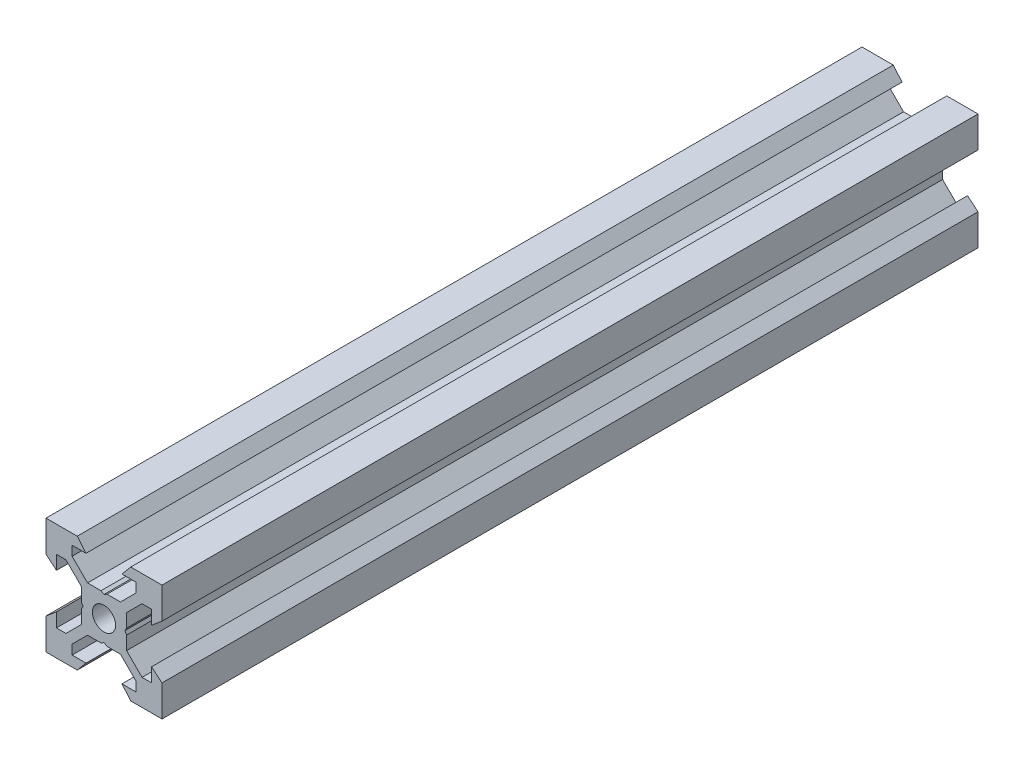
SolidWorks part; units mm, degrees
ref_plane "Front Plane" through (0, 0, 0) normal (0, 0, 1) x (1, 0, 0)
ref_plane "Top Plane" through (0, 0, 0) normal (0, 1, 0) x (1, 0, 0)
ref_plane "Right Plane" through (0, 0, 0) normal (1, 0, 0) x (0, 0, -1)
sketch "Sketch1" plane through (0, 0, 0) normal (0, 0, 1) x (1, 0, 0)
  line L0 (10, 10) -> (4.6104, 10) construction
  line L1 (10, 10) -> (10, 4.6104) construction
  line L2 (10, -10) -> (10, -4.6104) construction
  line L3 (10, -10) -> (4.6104, -10) construction
  line L4 (10, 10) -> (10, 4.6104)
  line L5 (6.5607, 5.5) -> (8.2, 5.5)
  line L6 (5.5, 8.2) -> (5.5, 6.5607)
  line L7 (10, 10) -> (4.6104, 10)
  line L8 (10, 10) -> (10, 4.6104)
  line L9 (6.5607, 5.5) -> (3.9, 2.8393)
  line L10 (5.5, 6.5607) -> (2.8393, 3.9)
  line L11 (10, 4.6104) -> (8.2, 3.1)
  line L12 (4.6104, 10) -> (3.1, 8.2)
  line L13 (8.2, 3.1) -> (8.2, 5.5)
  line L14 (3.1, 8.2) -> (5.5, 8.2)
  line L15 (-6.5607, 5.5) -> (-8.2, 5.5)
  line L16 (6.5607, -5.5) -> (8.2, -5.5)
  line L17 (3.1, -8.2) -> (5.5, -8.2)
  line L18 (8.2, -3.1) -> (8.2, -5.5)
  line L19 (4.6104, -10) -> (3.1, -8.2)
  line L20 (10, -4.6104) -> (8.2, -3.1)
  line L21 (0.5196, -3.9) -> (0, -3.6)
  line L22 (0.5196, 3.9) -> (0, 3.6)
  line L23 (3.6, 0) -> (3.9, -0.5196)
  line L24 (3.9, 0.5196) -> (3.6, 0)
  line L25 (3.9, 0.5196) -> (3.9, 2.8393)
  line L26 (2.8393, 3.9) -> (0.5196, 3.9)
  line L27 (3.9, -2.8393) -> (3.9, -0.5196)
  line L28 (2.8393, -3.9) -> (0.5196, -3.9)
  line L29 (5.5, -6.5607) -> (2.8393, -3.9)
  line L30 (6.5607, -5.5) -> (3.9, -2.8393)
  line L31 (10, -10) -> (10, -4.6104)
  line L32 (10, -10) -> (4.6104, -10)
  line L33 (5.5, -8.2) -> (5.5, -6.5607)
  line L34 (-6.5607, -5.5) -> (-8.2, -5.5)
  line L35 (10, -10) -> (10, -4.6104)
  line L36 (0, 0) -> (0, 8.2) construction
  line L37 (-10, -10) -> (-4.6104, -10) construction
  line L38 (-10, -10) -> (-10, -4.6104) construction
  line L39 (-10, 10) -> (-10, 4.6104) construction
  line L40 (-10, 10) -> (-4.6104, 10) construction
  line L41 (-10, -10) -> (-10, -4.6104)
  line L43 (-5.5, -8.2) -> (-5.5, -6.5607)
  line L44 (-10, -10) -> (-4.6104, -10)
  line L45 (-10, -10) -> (-10, -4.6104)
  line L46 (-6.5607, -5.5) -> (-3.9, -2.8393)
  line L47 (-5.5, -6.5607) -> (-2.8393, -3.9)
  line L48 (-2.8393, -3.9) -> (-0.5196, -3.9)
  line L49 (-3.9, -2.8393) -> (-3.9, -0.5196)
  line L50 (-2.8393, 3.9) -> (-0.5196, 3.9)
  line L51 (-3.9, 0.5196) -> (-3.9, 2.8393)
  line L52 (-3.9, 0.5196) -> (-3.6, 0)
  line L53 (-3.6, 0) -> (-3.9, -0.5196)
  line L54 (-0.5196, 3.9) -> (0, 3.6)
  line L55 (-0.5196, -3.9) -> (0, -3.6)
  line L56 (-10, -4.6104) -> (-8.2, -3.1)
  line L57 (-4.6104, -10) -> (-3.1, -8.2)
  line L58 (-8.2, -3.1) -> (-8.2, -5.5)
  line L59 (-3.1, -8.2) -> (-5.5, -8.2)
  line L60 (-10, -10) -> (10, -10) construction
  line L61 (-10, -10) -> (-10, 10) construction
  line L62 (-3.1, 8.2) -> (-5.5, 8.2)
  line L63 (-8.2, 3.1) -> (-8.2, 5.5)
  line L64 (-4.6104, 10) -> (-3.1, 8.2)
  line L65 (-10, 4.6104) -> (-8.2, 3.1)
  line L66 (-5.5, 6.5607) -> (-2.8393, 3.9)
  line L67 (-6.5607, 5.5) -> (-3.9, 2.8393)
  line L68 (-10, 10) -> (-10, 4.6104)
  line L69 (-10, 10) -> (-4.6104, 10)
  line L70 (-5.5, 8.2) -> (-5.5, 6.5607)
  line L71 (-10, 10) -> (10, 10) construction
  line L72 (-10, 10) -> (-10, 4.6104)
  line L73 (10, -10) -> (10, 10) construction
  line L74 (-10, -10) -> (10, 10) construction
  line L75 (-10, 10) -> (10, -10) construction
  circle A0 centre (0, 0) radius 2
  dimension "D7" = 4
  dimension "D1" = 20
  dimension "D2" = 5.3896
  dimension "D3" = 4.5
  dimension "D4" = 50
  dimension "D5" = 1.8
  dimension "D6" = 1.5104
  dimension "D8" = 5.5
  dimension "D9" = 120
  dimension "D10" = 0.3
  dimension "D11" = 2.3197
  dimension "D12" = 7.8
  dimension "D13" = 7.8
  dimension "D14" = 1.5
  dimension "D15" = 2.6607
extrude "Boss-Extrude1" add sketch "Sketch1" along normal mid plane 140.71 contours L70 L62 L64 L69 L68 L65 L63 L15 L67 L51 L52 L53 L49 L46 L34 L58 L56 L41 L44 L57 L59 L43 L47 L48 L55 L21 L28 L29 L33 L17 L19 L32 L31 L20 L18 L16 L30 L27 L23 L24 L25 L9 L5 L13 L11 L4 L7 L12 L14 L6 L10
